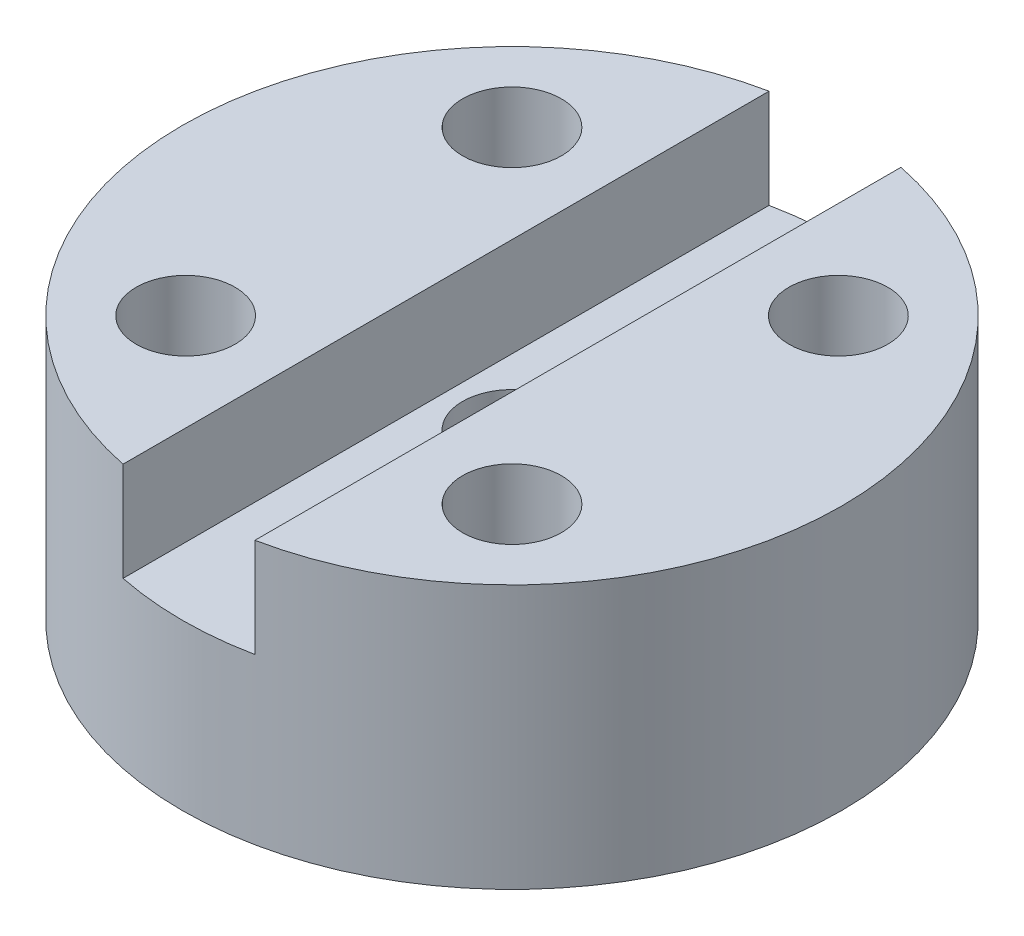
SolidWorks part; units mm, degrees
ref_plane "Ebene vorne" through (0, 0, 0) normal (0, 0, 1) x (1, 0, 0)
ref_plane "Ebene oben" through (0, 0, 0) normal (0, 1, 0) x (1, 0, 0)
ref_plane "Ebene rechts" through (0, 0, 0) normal (1, 0, 0) x (0, 0, -1)
sketch "Skizze1" plane through (0, 0, 0) normal (0, 1, 0) x (1, 0, 0)
  line L1 (-4.9497, 4.9497) -> (4.9497, 4.9497) construction
  line L2 (-4.9497, 4.9497) -> (-4.9497, -4.9497) construction
  line L3 (-4.9497, -4.9497) -> (4.9497, -4.9497) construction
  line L4 (4.9497, 4.9497) -> (4.9497, -4.9497) construction
  line L5 (-4.9497, 4.9497) -> (4.9497, -4.9497) construction
  line L6 (-4.9497, -4.9497) -> (4.9497, 4.9497) construction
  circle A0 centre (0, 0) radius 10
  circle A1 centre (4.9497, 4.9497) radius 1.5
  circle A2 centre (-4.9497, 4.9497) radius 1.5
  circle A3 centre (-4.9497, -4.9497) radius 1.5
  circle A4 centre (4.9497, -4.9497) radius 1.5
  circle A5 centre (0, 0) radius 1.5
  dimension "D1" = 20
  dimension "D3" = 3
  dimension "D2" = 14
extrude "Aufsatz-Linear austragen1" add sketch "Skizze1" along normal blind 8
sketch "Skizze2" plane through (0, 8, 0) normal (0, 1, 0) x (1, 0, 0)
  line L1 (-2, 11.3682) -> (2, 11.3682)
  line L2 (-2, 11.3682) -> (-2, -11.3682)
  line L3 (-2, -11.3682) -> (2, -11.3682)
  line L4 (2, 11.3682) -> (2, -11.3682)
  line L5 (-2, 11.3682) -> (2, -11.3682) construction
  line L6 (-2, -11.3682) -> (2, 11.3682) construction
  point P0 (0, 0)
  dimension "D1" = 4
extrude "Schnitt-Linear austragen1" cut sketch "Skizze2" against normal blind 3
sketch "Skizze3" plane through (0, 0, 0) normal (0, -1, 0) x (1, 0, 0)
  circle A0 centre (0, 0) radius 3.5
  dimension "D1" = 7
extrude "Schnitt-Linear austragen2" cut sketch "Skizze3" against normal blind 3
